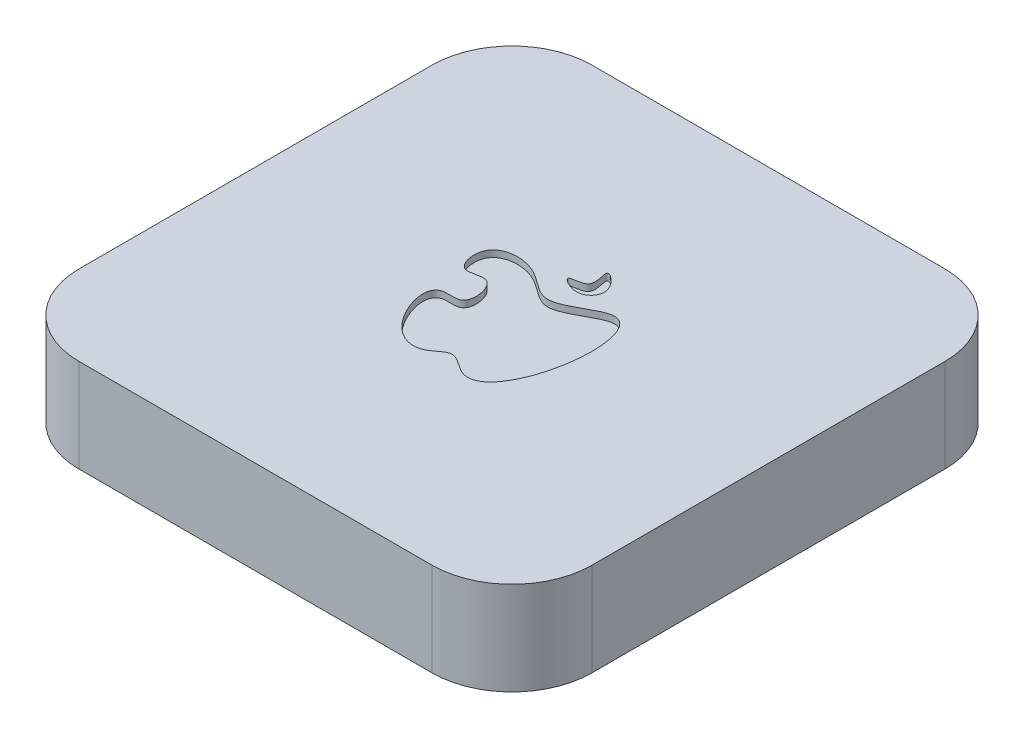
SolidWorks part; units mm, degrees
ref_plane "Front Plane" through (0, 0, 0) normal (0, 0, 1) x (1, 0, 0)
ref_plane "Top Plane" through (0, 0, 0) normal (0, 1, 0) x (1, 0, 0)
ref_plane "Right Plane" through (0, 0, 0) normal (1, 0, 0) x (0, 0, -1)
sketch "Sketch1" plane through (0, 0, 0) normal (0, 1, 0) x (1, 0, 0)
  line L1 (-67.31, -97.79) -> (67.31, -97.79)
  line L2 (-97.79, -67.31) -> (-97.79, 67.31)
  line L3 (-67.31, 97.79) -> (67.31, 97.79)
  line L4 (97.79, -67.31) -> (97.79, 67.31)
  line L5 (-97.79, -97.79) -> (97.79, 97.79) construction
  line L6 (-97.79, 97.79) -> (97.79, -97.79) construction
  arc A0 (67.31, 97.79) -> (97.79, 67.31) centre (67.31, 67.31) cw
  arc A1 (97.79, -67.31) -> (67.31, -97.79) centre (67.31, -67.31) cw
  arc A2 (-67.31, -97.79) -> (-97.79, -67.31) centre (-67.31, -67.31) cw
  arc A3 (-97.79, 67.31) -> (-67.31, 97.79) centre (-67.31, 67.31) cw
  point P0 (0, 0)
  dimension "D3" = 30.48
  dimension "D1" = 195.58
  dimension "D2" = 195.58
extrude "Boss-Extrude1" add sketch "Sketch1" along normal blind 35.56
sketch "Sketch2" plane through (0, 35.56, 0) normal (0, 1, 0) x (1, 0, 0)
  spline S0 degree 3 poles (-10.1256, 21.7962) (1.2, 6.0136) (25.3109, 29.2342) (30.491, -7.917) (15.0268, -36.1095) (1.5308, -21.8353) (-6.0406, -30.6126) (-20.6584, -26.8465) (-28.2677, -2.5017) (-10.9023, -7.0583) (-14.0441, 10.3996) (-25.9145, 3.073) (-29.5077, 20.4211) (-10.1256, 21.7962) (1.2, 6.0136) (25.3109, 29.2342) knots -0.211415 -0.158965 -0.079811 0 0.107274 0.250434 0.39598 0.443398 0.478949 0.546713 0.653285 0.688805 0.749021 0.788585 0.841035 0.920189 1 1.107274 1.250434 1.39598 only from (1.0692, 12.054) to (1.0692, 12.054)
  spline S1 degree 3 poles (7.5836, 23.0148) (1.3687, 35.8863) (13.3028, 26.0546) (5.9761, 17.4683) (-5.1634, 24.0841) (7.5836, 23.0148) (1.3687, 35.8863) (13.3028, 26.0546) knots -0.545054 -0.365222 -0.195831 0 0.216217 0.454946 0.634778 0.804169 1 1.216217 1.454946 1.634778 only from (4.2882, 31.9686) to (4.2882, 31.9686)
extrude "Cut-Extrude1" cut sketch "Sketch2" against normal blind 2.54
